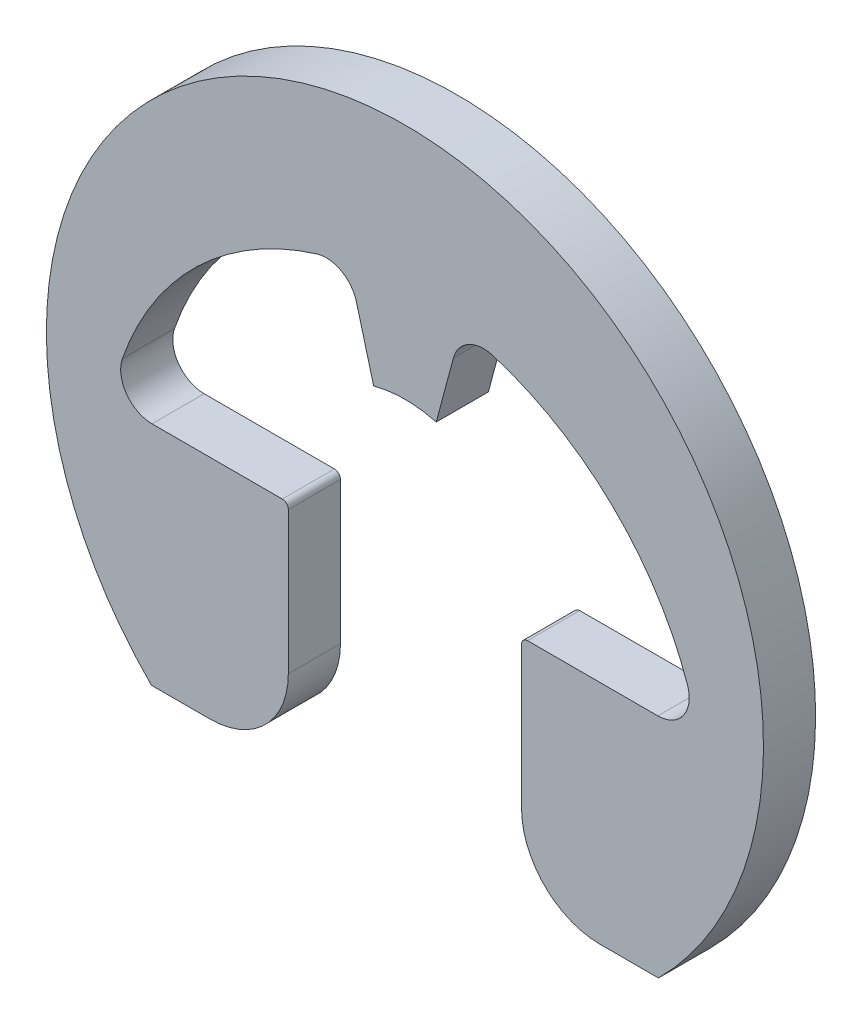
SolidWorks part; units mm, degrees
ref_plane "Plane1" through (0, 0, 0) normal (0, 0, 1) x (1, 0, 0)
ref_plane "Plane2" through (0, 0, 0) normal (0, 1, 0) x (1, 0, 0)
ref_plane "Plane3" through (0, 0, 0) normal (1, 0, 0) x (0, 0, -1)
other "Configuration Table"
sketch "Clipboard" plane through (0, 0, 0) normal (0, 0, 1) x (1, 0, 0)
  line L0 (0, 0) -> (1.7366, 0)
  circle A0 centre (0, 0) radius 1.4351
  circle A1 centre (0, 0) radius 4.2545
  dimension "FreeID" = 2.8702
  dimension "FreeOD" = 8.509
  dimension "LargeSection" = 1.7366
sketch "BodySke" plane through (0, 0, 0) normal (0, 0, 1) x (1, 0, 0)
  line L0 (-3.4992, 0) -> (3.4992, 0) construction
  line L1 (0, 0) -> (0, 2.6309) construction
  line L2 (0, 0) -> (0.1962, 0.7323) construction
  line L3 (0, 0) -> (4.2186, -1.1304) construction
  line L4 (0, 0) -> (-0.1962, 0.7323) construction
  line L5 (0, 0) -> (-4.2186, -1.1304) construction
  line L6 (0, 0) -> (3.0883, -3.0883) construction
  line L7 (0, 0) -> (-3.0883, -3.0883) construction
  line L8 (3.0883, -3.0883) -> (2.3756, -3.0883)
  line L9 (-2.3756, -3.0883) -> (-3.0883, -3.0883)
  line L10 (1.4942, -0.3267) -> (3.0809, -0.3267)
  line L11 (0.5904, 2.2034) -> (0.3813, 1.423)
  line L12 (-0.5904, 2.2034) -> (-0.3813, 1.423)
  line L13 (1.4205, -0.4004) -> (1.4205, -2.1332)
  line L14 (-1.4942, -0.3267) -> (-3.0809, -0.3267)
  line L15 (-1.4205, -0.4004) -> (-1.4205, -2.1332)
  circle A0 centre (0, 0) radius 1.4732 construction
  arc A1 (3.4992, 0) -> (-3.4992, 0) centre (0, -1.0116) ccw construction
  arc A2 (3.0883, -3.0883) -> (-3.0883, -3.0883) centre (0, 0) ccw
  arc A3 (1.4942, -0.3267) -> (1.4205, -0.4004) centre (1.4942, -0.4004) ccw
  arc A4 (-1.4205, -0.4004) -> (-1.4942, -0.3267) centre (-1.4942, -0.4004) ccw
  arc A5 (-3.4419, 0.1804) -> (-1.0718, 2.4696) centre (0, -1.0116) cw
  arc A6 (-0.3813, 1.423) -> (0.3813, 1.423) centre (0, 0) cw
  arc A7 (1.0718, 2.4696) -> (3.4419, 0.1804) centre (0, -1.0116) cw
  arc A8 (3.0809, -0.3267) -> (3.4419, 0.1804) centre (3.0809, 0.0553) ccw
  arc A9 (1.0718, 2.4696) -> (0.5904, 2.2034) centre (0.9594, 2.1045) ccw
  arc A10 (-0.5904, 2.2034) -> (-1.0718, 2.4696) centre (-0.9594, 2.1045) ccw
  arc A11 (-3.4419, 0.1804) -> (-3.0809, -0.3267) centre (-3.0809, 0.0553) ccw
  arc A12 (1.4205, -2.1332) -> (2.3756, -3.0883) centre (2.3756, -2.1332) ccw
  arc A13 (-2.3756, -3.0883) -> (-1.4205, -2.1332) centre (-2.3756, -2.1332) ccw
  dimension "GrooveDia" = 2.9464
  dimension "OutsideDia" = 8.7349
  dimension "InnerTipRad" = 0.0737
  dimension "CavityFilletRad" = 0.382
  dimension "OuterTipRadius" = 0.9551
  dimension "D3" = 30
  dimension "D1" = 15
  dimension "CavityWidth" = 6.9984
  dimension "CavityHeight" = 2.6309
extrude "Body" add sketch "BodySke" against normal blind 0.635
equation "' \"FreeID@Clipboard\" = 0.072"
equation "' \"Thickness@Body\" = 0.015"
equation "' \"GrooveDia@BodySke\" = 0.074"
equation "' \"FreeOD@Clipboard\" = 0.206"
equation "' \"FreeID@Clipboard\" = 0.430"
equation "' \"Thickness@Body\" = 0.042"
equation "' \"GrooveDia@BodySke\" = 0.437"
equation "' \"FreeOD@Clipboard\" = 0.870"
equation "\"OutsideDia@BodySke\" = ( \"GrooveDia@BodySke\"  /  \"FreeID@Clipboard\" )  * \"FreeOD@Clipboard\""
equation "\"LargeSection@Clipboard\" =  (\"OutsideDia@BodySke\" - \"GrooveDia@BodySke\") / 2 * 0.6"
equation "\"CavityHeight@BodySke\" = \"OutsideDia@BodySke\"  /  2 - \"LargeSection@Clipboard\""
equation "\"CavityWidth@BodySke\" = \"OutsideDia@BodySke\" -  \"LargeSection@Clipboard\""
equation "\"CavityFilletRad@BodySke\" =  (\"CavityHeight@BodySke\" * 2 - \"GrooveDia@BodySke\") / 2 * 0.33"
equation "\"InnerTipRad@BodySke\" = \"GrooveDia@BodySke\" * 0.025"
equation "\"OuterTipRadius@BodySke\" =  (\"OutsideDia@BodySke\" - \"GrooveDia@BodySke\") / 2 * 0.33"
